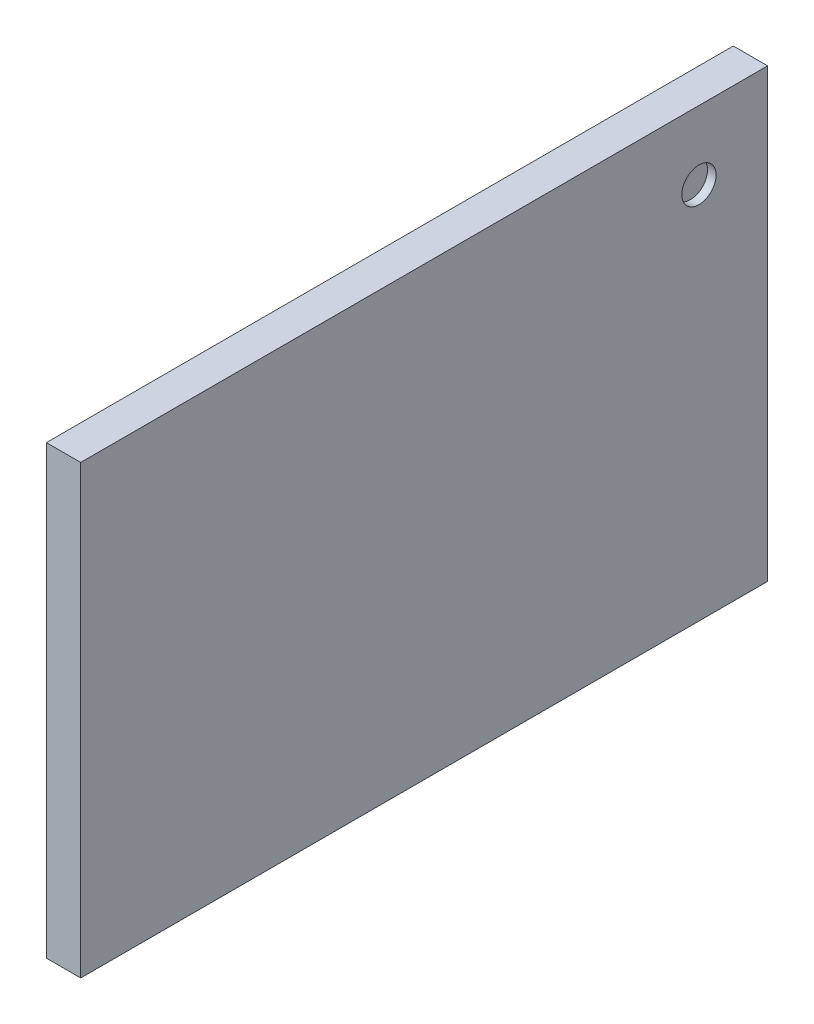
SolidWorks part; units mm, degrees
material "1060 Alloy"
ref_plane "Front Plane" through (0, 0, 0) normal (0, 0, 1) x (1, 0, 0)
ref_plane "Top Plane" through (0, 0, 0) normal (0, 1, 0) x (1, 0, 0)
ref_plane "Right Plane" through (0, 0, 0) normal (1, 0, 0) x (0, 0, -1)
sketch "Sketch1" plane through (0, 0, 0) normal (1, 0, 0) x (0, 0, -1)
  line L1 (-466.8184, 26.8007) -> (41.1816, 26.8007)
  line L2 (-466.8184, 26.8007) -> (-466.8184, -303.3993)
  line L3 (-466.8184, -303.3993) -> (41.1816, -303.3993)
  line L4 (41.1816, 26.8007) -> (41.1816, -303.3993)
  dimension "D1" = 508
  dimension "D2" = 330.2
  dimension "D3" = 41.1816
  dimension "D4" = 26.8007
extrude "Boss-Extrude1" add sketch "Sketch1" along normal blind 25.4
sketch "Sketch2" plane through (25.4, 0, 0) normal (1, 0, 0) x (0, 0, -1)
  line L0 (41.1816, 26.8007) -> (-466.8184, 26.8007) construction
  line L1 (41.1816, -303.3993) -> (41.1816, 26.8007) construction
  circle A0 centre (-9.6184, -23.9993) radius 12.7
  dimension "D1" = 25.4
  dimension "D2" = 50.8
  dimension "D3" = 50.8
extrude "Cut-Extrude1" cut sketch "Sketch2" against normal blind 6.35
